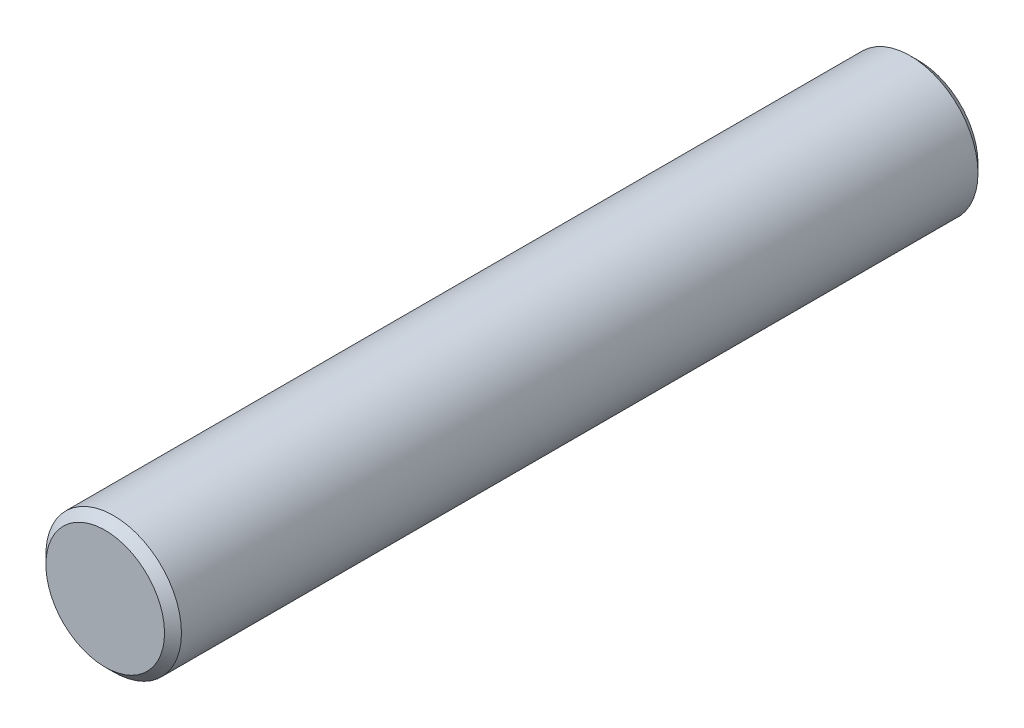
SolidWorks part; units mm, degrees
ref_plane "Front Plane" through (0, 0, 0) normal (0, 0, 1) x (1, 0, 0)
ref_plane "Top Plane" through (0, 0, 0) normal (0, 1, 0) x (1, 0, 0)
ref_plane "Right Plane" through (0, 0, 0) normal (1, 0, 0) x (0, 0, -1)
sketch "Sketch2" plane through (0, 0, 0) normal (0, 0, 1) x (1, 0, 0)
  circle A0 centre (0, 0) radius 8
  dimension "D1" = 16
extrude "Boss-Extrude1" add sketch "Sketch2" along normal mid plane 96
chamfer "Chamfer1" distance 1 angle 45 2 edges at (8, 0, -48) (8, 0, 48)
